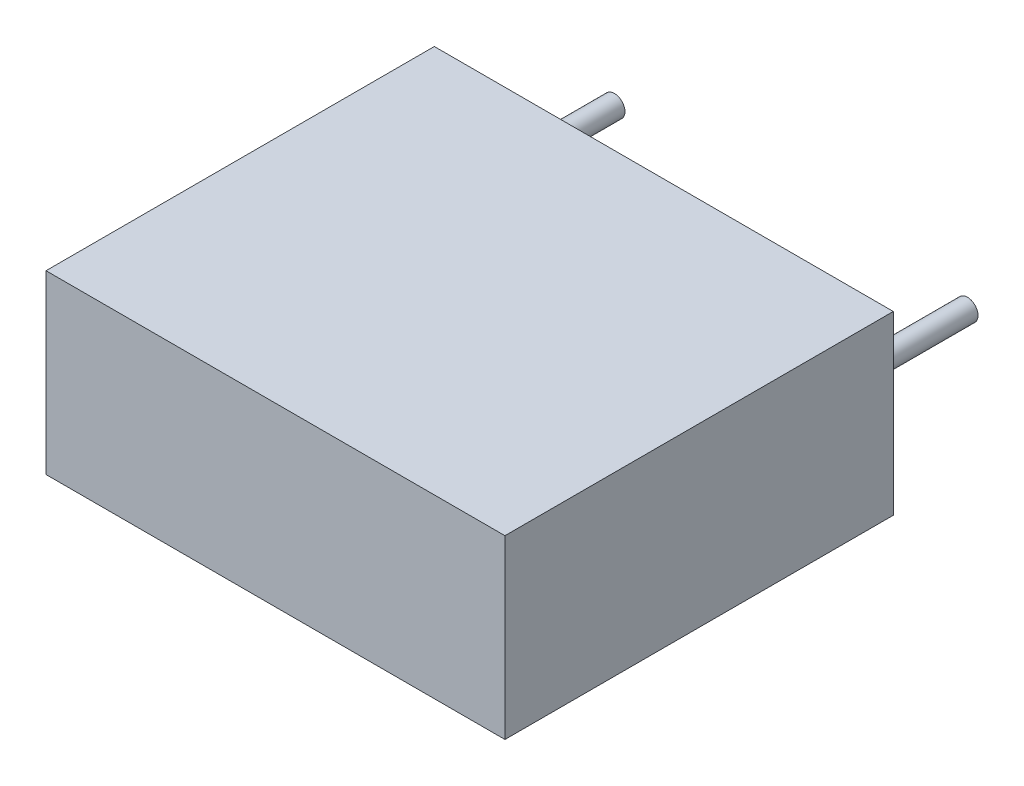
SolidWorks part; units mm, degrees
ref_plane "Plan de face" through (0, 0, 0) normal (0, 0, 1) x (1, 0, 0)
ref_plane "Plan de dessus" through (0, 0, 0) normal (0, 1, 0) x (1, 0, 0)
ref_plane "Plan de droite" through (0, 0, 0) normal (1, 0, 0) x (0, 0, -1)
sketch "Esquisse1" plane through (0, 0, 0) normal (0, 0, 1) x (1, 0, 0)
  line L1 (-6.5, -2.5) -> (6.5, -2.5)
  line L2 (-6.5, -2.5) -> (-6.5, 2.5)
  line L3 (-6.5, 2.5) -> (6.5, 2.5)
  line L4 (6.5, -2.5) -> (6.5, 2.5)
  line L5 (-6.5, -2.5) -> (6.5, 2.5) construction
  line L6 (-6.5, 2.5) -> (6.5, -2.5) construction
  point P0 (0, 0)
  dimension "D1" = 5
  dimension "D2" = 13
extrude "Boss.-Extru.1" add sketch "Esquisse1" along normal blind 11
sketch "Esquisse2" plane through (0, 0, 0) normal (0, 0, -1) x (-1, 0, 0)
  line L0 (-5, 0) -> (0, 0) construction
  line L1 (0, 0) -> (5, 0) construction
  circle A0 centre (-5, 0) radius 0.3
  circle A1 centre (5, 0) radius 0.3
  dimension "D1" = 0.6
  dimension "D2" = 10
extrude "Boss.-Extru.2" add sketch "Esquisse2" along normal blind 3.6
